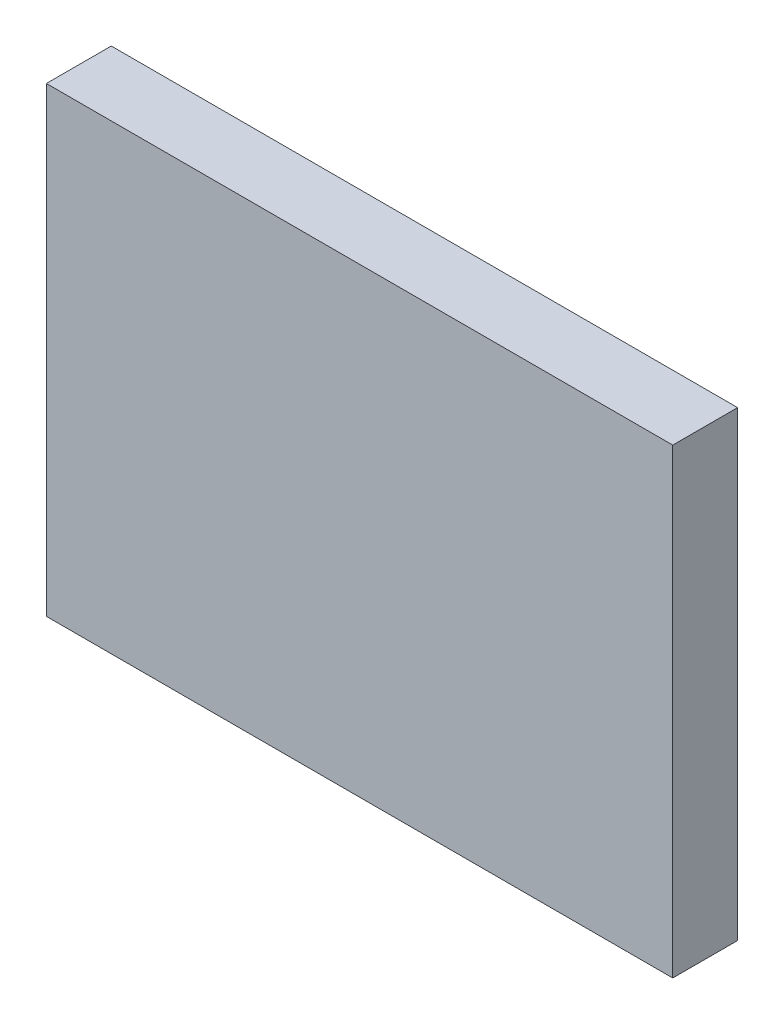
SolidWorks part; units mm, degrees
ref_plane "Front Plane" through (0, 0, 0) normal (0, 0, 1) x (1, 0, 0)
ref_plane "Top Plane" through (0, 0, 0) normal (0, 1, 0) x (1, 0, 0)
ref_plane "Right Plane" through (0, 0, 0) normal (1, 0, 0) x (0, 0, -1)
sketch "Sketch1" plane through (0, 0, 0) normal (0, 0, 1) x (1, 0, 0)
  line L0 (-4.826, 3.556) -> (4.826, 3.556)
  line L1 (4.826, 3.556) -> (4.826, -3.556)
  line L2 (4.826, -3.556) -> (-4.826, -3.556)
  line L3 (-4.826, -3.556) -> (-4.826, 3.556)
extrude "Component_Outline" add sketch "Sketch1" along normal blind 1 separate body
sketch3d "3DSketch1"
  line L0 (0, 0, 0) -> (1, 0, 0)
  line L1 (0, 0, 0) -> (0, 1, 0)
  line L2 (0, 0, 0) -> (0, 0, 1)
  point P0 (0, 0, 0)
